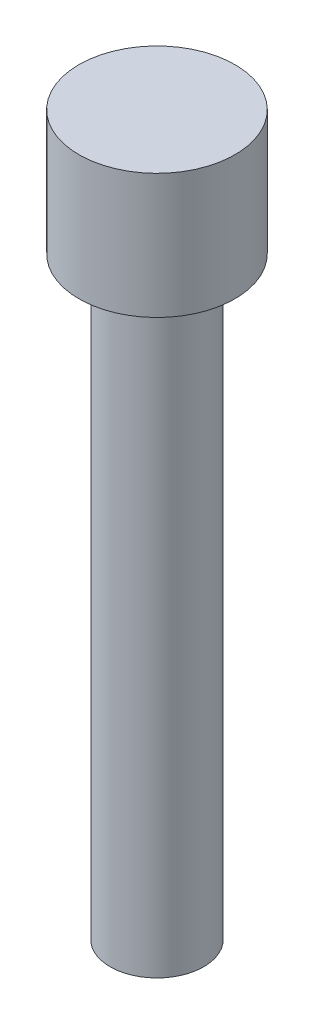
SolidWorks part; units mm, degrees
ref_plane "Front Plane" through (0, 0, 0) normal (0, 0, 1) x (1, 0, 0)
ref_plane "Top Plane" through (0, 0, 0) normal (0, 1, 0) x (1, 0, 0)
ref_plane "Right Plane" through (0, 0, 0) normal (1, 0, 0) x (0, 0, -1)
sketch "Sketch1" plane through (0, 238.5931, 0) normal (0, 1, 0) x (1, 0, 0)
  circle A0 centre (-59.3995, -183.81) radius 1.5
extrude "Boss-Extrude1" add sketch "Sketch1" against normal blind 7 and the other way up to surface (12.033 mm away)
sketch "Sketch2" plane through (0, 250.6261, 0) normal (0, 1, 0) x (1, 0, 0)
  circle A0 centre (-59.3995, -183.81) radius 2.5
  dimension "D1" = 5
extrude "Boss-Extrude2" add sketch "Sketch2" along normal blind 4 contours A0
